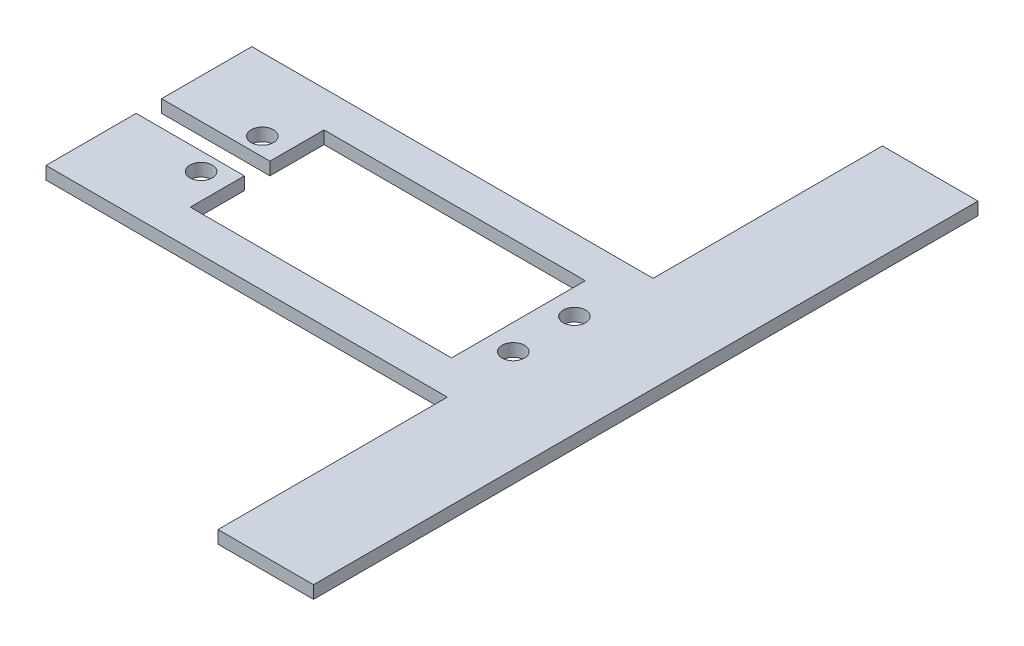
SolidWorks part; units mm, degrees
ref_plane "Front Plane" through (0, 0, 0) normal (0, 0, 1) x (1, 0, 0)
ref_plane "Top Plane" through (0, 0, 0) normal (0, 1, 0) x (1, 0, 0)
ref_plane "Right Plane" through (0, 0, 0) normal (1, 0, 0) x (0, 0, -1)
sketch "Sketch1" plane through (0, 0, 0) normal (0, 1, 0) x (1, 0, 0)
  line L0 (-24.5, -4.8) -> (-24.5, 4.8) construction
  line L1 (-37.5, 16.15) -> (25.5, 16.15)
  line L2 (-37.5, 16.15) -> (-37.5, 2)
  line L3 (-37.5, -16.15) -> (25.5, -16.15)
  line L5 (-37.5, -2) -> (-37.5, -16.15)
  line L6 (-20.5, 10.5) -> (20.5, 10.5)
  line L7 (-20.5, 10.5) -> (-20.5, 2)
  line L8 (-20.5, -10.5) -> (20.5, -10.5)
  line L9 (20.5, 10.5) -> (20.5, -10.5)
  line L10 (-20.5, 10.5) -> (20.5, -10.5) construction
  line L11 (-20.5, -10.5) -> (20.5, 10.5) construction
  line L12 (-20.5, 2) -> (-37.5, 2)
  line L14 (-20.5, -2) -> (-37.5, -2)
  line L16 (-20.5, -2) -> (-20.5, -10.5)
  line L17 (0, 16.15) -> (0, -16.15) construction
  line L18 (25.5, -16.15) -> (25.5, -52.15)
  line L19 (25.5, 52.15) -> (40.5, 52.15)
  line L20 (25.5, 52.15) -> (25.5, 16.15)
  line L21 (25.5, -52.15) -> (40.5, -52.15)
  line L22 (40.5, 52.15) -> (40.5, -52.15)
  line L23 (25.5, 52.15) -> (40.5, -52.15) construction
  line L24 (25.5, -52.15) -> (40.5, 52.15) construction
  circle A0 centre (-24.5, 4.8) radius 1.75
  circle A1 centre (-24.5, -4.8) radius 1.75
  circle A2 centre (24.5, -4.8) radius 1.75
  circle A3 centre (24.5, 4.8) radius 1.75
  point P0 (0, 0)
  point P8 (0, 0)
  point P14 (-20.8968, 0)
  point P20 (-24.5, 0)
  point P24 (0, 0)
  point P30 (33, 0)
  dimension "D7" = 3.5
  dimension "D1" = 32.3
  dimension "D2" = 21
  dimension "D3" = 41
  dimension "D4" = 17
  dimension "D5" = 4
  dimension "D6" = 9.6
  dimension "D8" = 4
  dimension "D9" = 20
  dimension "D10" = 15
  dimension "D11" = 36
extrude "Boss-Extrude1" add sketch "Sketch1" along normal blind 2
